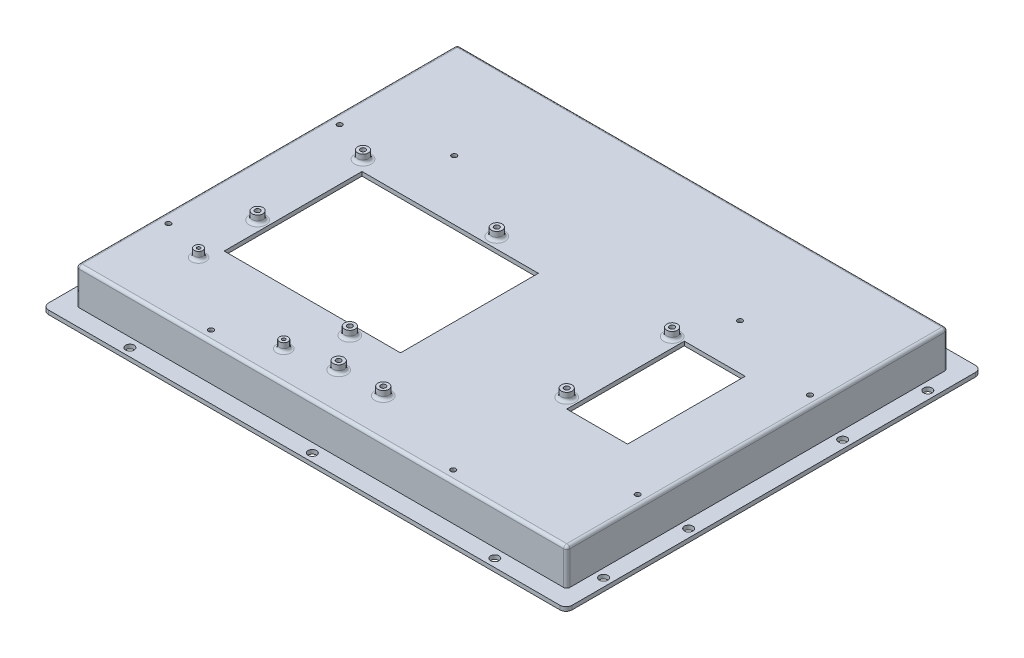
SolidWorks part; units mm, degrees
ref_plane "Front Plane" through (0, 0, 0) normal (0, 0, 1) x (1, 0, 0)
ref_plane "Top Plane" through (0, 0, 0) normal (0, 1, 0) x (1, 0, 0)
ref_plane "Right Plane" through (0, 0, 0) normal (1, 0, 0) x (0, 0, -1)
sketch "Sketch1" plane through (0, 0, 0) normal (0, 1, 0) x (1, 0, 0)
  line L1 (0, 0) -> (258.3, 0)
  line L2 (0, 0) -> (0, 205)
  line L3 (0, 205) -> (258.3, 205)
  line L4 (258.3, 0) -> (258.3, 205)
  dimension "D1" = 258.3
  dimension "D2" = 205
extrude "Boss-Extrude1" add sketch "Sketch1" along normal blind 20
sketch "Sketch2" plane through (0, 20, 0) normal (0, 1, 0) x (-1, 0, 0)
  line L0 (-129.15, 0) -> (-129.15, 18.2552) construction
  line L1 (-8.15, -8.5) -> (-250.15, -8.5)
  line L2 (-8.15, -8.5) -> (-8.15, -196.5)
  line L3 (-8.15, -196.5) -> (-250.15, -196.5)
  line L4 (-250.15, -8.5) -> (-250.15, -196.5)
  line L5 (0, 0) -> (-258.3, 0) construction
  line L6 (-258.3, -102.5) -> (-281.1398, -102.5) construction
  line L7 (-258.3, 0) -> (-258.3, -205) construction
  dimension "D1" = 242
  dimension "D2" = 188
extrude "Cut-Extrude1" cut sketch "Sketch2" against normal blind 18 flip side to cut
sketch "Sketch3" plane through (0, 0, 0) normal (0, -1, 0) x (1, 0, 0)
  line L0 (258.3, -102.5) -> (287.3168, -102.5) construction
  line L1 (248.15, -194.5) -> (10.15, -194.5)
  line L2 (248.15, -194.5) -> (248.15, -10.5)
  line L3 (248.15, -10.5) -> (10.15, -10.5)
  line L4 (10.15, -194.5) -> (10.15, -10.5)
  line L5 (258.3, 0) -> (258.3, -205) construction
  line L6 (129.15, -205) -> (129.15, -238.7281) construction
  line L8 (258.3, -205) -> (0, -205) construction
  dimension "D1" = 238
  dimension "D2" = 184
extrude "Cut-Extrude2" cut sketch "Sketch3" against normal blind 18
sketch "Sketch4" plane through (0, 20, 0) normal (0, 1, 0) x (1, 0, 0)
  line L0 (8.15, 196.5) -> (8.15, 8.5) construction
  line L1 (126.15, 50.5) -> (39.15, 50.5)
  line L2 (126.15, 50.5) -> (126.15, 118.5)
  line L3 (126.15, 118.5) -> (39.15, 118.5)
  line L4 (39.15, 50.5) -> (39.15, 118.5)
  line L5 (221.15, 67.5) -> (191.15, 67.5)
  line L6 (221.15, 67.5) -> (221.15, 125.5)
  line L7 (221.15, 125.5) -> (191.15, 125.5)
  line L8 (191.15, 67.5) -> (191.15, 125.5)
  line L9 (8.15, 8.5) -> (250.15, 8.5) construction
  line L10 (250.15, 8.5) -> (250.15, 196.5) construction
  dimension "D1" = 31
  dimension "D2" = 87
  dimension "D3" = 42
  dimension "D4" = 68
  dimension "D5" = 30
  dimension "D6" = 58
  dimension "D7" = 59
  dimension "D8" = 29
extrude "Cut-Extrude3" cut sketch "Sketch4" against normal through all
sketch "Sketch5" plane through (0, 20, 0) normal (0, 1, 0) x (1, 0, 0)
  line L0 (39.15, 50.5) -> (126.15, 50.5) construction
  line L1 (126.15, 50.5) -> (126.15, 118.5) construction
  line L2 (8.15, 8.5) -> (250.15, 8.5) construction
  line L3 (39.15, 118.5) -> (39.15, 50.5) construction
  line L4 (191.15, 125.5) -> (191.15, 67.5) construction
  line L5 (191.15, 67.5) -> (221.15, 67.5) construction
  line L6 (8.15, 196.5) -> (8.15, 8.5) construction
  circle A0 centre (34.15, 72) radius 2.65
  circle A1 centre (34.15, 124) radius 2.65
  circle A2 centre (100.15, 124) radius 2.65
  circle A3 centre (106.15, 45.5) radius 2.65
  circle A4 centre (186.15, 72.5) radius 2.65
  circle A5 centre (186.15, 124.5) radius 2.65
  circle A6 centre (118.15, 28) radius 2.65
  circle A7 centre (140.15, 28) radius 2.65
  dimension "D1" = 5.3
  dimension "D4" = 5
  dimension "D5" = 20
  dimension "D7" = 5
  dimension "D8" = 52
  dimension "D9" = 5
  dimension "D10" = 5
  dimension "D13" = 110
  dimension "D2" = 52
  dimension "D3" = 66
  dimension "D6" = 21.5
  dimension "D11" = 22
  dimension "D12" = 19.5
extrude "Boss-Extrude2" add sketch "Sketch5" along normal blind 4
sketch "Sketch6" plane through (0, 24, 0) normal (0, 1, 0) x (1, 0, 0)
  circle A0 centre (34.15, 124) radius 1.25
  circle A1 centre (100.15, 124) radius 1.25
  circle A2 centre (186.15, 124.5) radius 1.25
  circle A3 centre (186.15, 72.5) radius 1.25
  circle A4 centre (106.15, 45.5) radius 1.25
  circle A5 centre (34.15, 72) radius 1.25
  circle A6 centre (140.15, 28) radius 1.25
  circle A7 centre (118.15, 28) radius 1.25
  dimension "D1" = 2.5
extrude "Cut-Extrude4" cut sketch "Sketch6" against normal through all
sketch "Sketch7" plane through (0, 2, 0) normal (0, 1, 0) x (1, 0, 0)
  line L0 (0, 0) -> (258.3, 0) construction
  line L1 (258.3, 0) -> (258.3, 205) construction
  line L2 (0, 205) -> (0, 0) construction
  line L3 (258.3, 205) -> (0, 205) construction
  line L4 (258.3, 205) -> (0, 205) construction
  line L5 (129.15, 0) -> (129.15, -15.0933) construction
  line L7 (258.3, 102.5) -> (279.2876, 102.5) construction
  line L8 (0, 102.5) -> (-38.7144, 102.5) construction
  line L9 (129.15, 205) -> (129.15, 223.317) construction
  circle A0 centre (254.3, 22.5) radius 2.1
  circle A1 centre (254.3, 140.5) radius 2.1
  circle A2 centre (254.3, 182.5) radius 2.1
  circle A4 centre (219.15, 201) radius 2.1
  circle A5 centre (134.15, 201) radius 2.1
  circle A6 centre (124.15, 201) radius 2.1
  circle A7 centre (39.15, 201) radius 2.1
  circle A9 centre (4, 182.5) radius 2.1
  circle A10 centre (4, 102.5) radius 2.1
  circle A11 centre (4, 22.5) radius 2.1
  circle A12 centre (219.15, 4) radius 2.1
  circle A13 centre (129.15, 4) radius 2.1
  circle A14 centre (39.15, 4) radius 2.1
  circle A15 centre (254.3, 64.5) radius 2.1
  dimension "D1" = 4.2
  dimension "D2" = 4
  dimension "D3" = 4
  dimension "D6" = 90
  dimension "D7" = 90
  dimension "D13" = 10
  dimension "D14" = 4.2
  dimension "D16" = 85
  dimension "D4" = 4
  dimension "D5" = 4
  dimension "D8" = 42
  dimension "D9" = 42
  dimension "D10" = 76
  dimension "D11" = 80
  dimension "D12" = 80
extrude "Cut-Extrude5" cut sketch "Sketch7" against normal through all
sketch "Sketch8" plane through (0, 20, 0) normal (0, 1, 0) x (1, 0, 0)
  circle A0 centre (55.15, 148) radius 1.25
  circle A1 centre (13.65, 133) radius 1.25
  circle A2 centre (13.65, 48.5) radius 1.25
  circle A3 centre (69.65, 13.5) radius 1.25
  circle A4 centre (189.15, 13.5) radius 1.25
  circle A5 centre (245.15, 48.5) radius 1.25
  circle A6 centre (245.15, 133.5) radius 1.25
  circle A7 centre (196.15, 148) radius 1.25
  dimension "D1" = 2.5
extrude "Cut-Extrude6" cut sketch "Sketch8" against normal through all
sketch "Sketch9" plane through (0, 18, 0) normal (0, -1, 0) x (1, 0, 0)
  circle A0 centre (13.65, -48.5) radius 3
  circle A1 centre (69.65, -13.5) radius 3
  circle A2 centre (189.15, -13.5) radius 3
  circle A3 centre (245.15, -48.5) radius 3
  circle A4 centre (245.15, -133.5) radius 3
  circle A5 centre (196.15, -148) radius 3
  circle A6 centre (55.15, -148) radius 3
  circle A7 centre (13.65, -133) radius 3
  circle A8 centre (13.65, -133) radius 1.25
  circle A9 centre (55.15, -148) radius 1.25
  circle A10 centre (196.15, -148) radius 1.25
  circle A11 centre (245.15, -133.5) radius 1.25
  circle A12 centre (245.15, -48.5) radius 1.25
  circle A13 centre (189.15, -13.5) radius 1.25
  circle A14 centre (69.65, -13.5) radius 1.25
  circle A15 centre (13.65, -48.5) radius 1.25
  dimension "D1" = 6
extrude "Boss-Extrude5" add sketch "Sketch9" along normal blind 2 and the other way blind 1 separate body
sketch "Sketch10" plane through (0, 0, 0) normal (0, -1, 0) x (1, 0, 0)
  line L0 (129.15, -10.5) -> (129.15, 23.0959) construction
  line L1 (8.15, -8.25) -> (20.15, -8.25)
  line L2 (8.15, -8.25) -> (8.15, -23.25)
  line L3 (8.15, -23.25) -> (20.15, -23.25)
  line L4 (20.15, -8.25) -> (20.15, -23.25)
  line L5 (119.15, -8.25) -> (139.15, -8.25)
  line L6 (119.15, -8.25) -> (119.15, -20.25)
  line L7 (119.15, -20.25) -> (139.15, -20.25)
  line L8 (139.15, -8.25) -> (139.15, -20.25)
  line L9 (238.15, -8.25) -> (250.15, -8.25)
  line L10 (238.15, -8.25) -> (238.15, -23.25)
  line L11 (238.15, -23.25) -> (250.15, -23.25)
  line L12 (250.15, -8.25) -> (250.15, -23.25)
  line L13 (8.15, -181.75) -> (20.15, -181.75)
  line L14 (8.15, -181.75) -> (8.15, -196.75)
  line L15 (8.15, -196.75) -> (20.15, -196.75)
  line L16 (20.15, -181.75) -> (20.15, -196.75)
  line L17 (146.15, -184.75) -> (181.15, -184.75)
  line L18 (146.15, -184.75) -> (146.15, -196.75)
  line L19 (146.15, -196.75) -> (181.15, -196.75)
  line L20 (181.15, -184.75) -> (181.15, -196.75)
  line L21 (238.15, -181.75) -> (250.15, -181.75)
  line L22 (238.15, -181.75) -> (238.15, -196.75)
  line L23 (238.15, -196.75) -> (250.15, -196.75)
  line L24 (250.15, -181.75) -> (250.15, -196.75)
  line L25 (248.15, -10.5) -> (10.15, -10.5) construction
  line L26 (10.15, -102.5) -> (-14.0756, -102.5) construction
  line L27 (10.15, -10.5) -> (10.15, -194.5) construction
  line L28 (248.15, -194.5) -> (248.15, -10.5) construction
  line L29 (10.15, -60) -> (20.15, -60)
  line L30 (10.15, -60) -> (10.15, -75)
  line L31 (10.15, -75) -> (20.15, -75)
  line L32 (20.15, -60) -> (20.15, -75)
  line L33 (10.15, -130) -> (20.15, -130)
  line L34 (10.15, -130) -> (10.15, -145)
  line L35 (10.15, -145) -> (20.15, -145)
  line L36 (20.15, -130) -> (20.15, -145)
  line L37 (248.15, -60) -> (238.15, -60)
  line L38 (248.15, -60) -> (248.15, -75)
  line L39 (248.15, -75) -> (238.15, -75)
  line L40 (238.15, -60) -> (238.15, -75)
  line L41 (248.15, -10.5) -> (10.15, -10.5) construction
  line L42 (248.15, -130) -> (238.15, -130)
  line L43 (248.15, -130) -> (248.15, -145)
  line L44 (248.15, -145) -> (238.15, -145)
  line L45 (238.15, -130) -> (238.15, -145)
  line L46 (56.65, -10.5) -> (76.65, -10.5)
  line L47 (56.65, -10.5) -> (56.65, -20.25)
  line L48 (56.65, -20.25) -> (76.65, -20.25)
  line L49 (76.65, -10.5) -> (76.65, -20.25)
  line L50 (10.15, -194.5) -> (248.15, -194.5) construction
  line L51 (181.65, -10.5) -> (201.65, -10.5)
  line L52 (181.65, -10.5) -> (181.65, -20.25)
  line L53 (181.65, -20.25) -> (201.65, -20.25)
  line L54 (201.65, -10.5) -> (201.65, -20.25)
  line L55 (77.15, -194.5) -> (112.15, -194.5)
  line L56 (77.15, -194.5) -> (77.15, -184.75)
  line L57 (77.15, -184.75) -> (112.15, -184.75)
  line L58 (112.15, -194.5) -> (112.15, -184.75)
  line L59 (10.15, -194.5) -> (248.15, -194.5) construction
  line L60 (218.15, -194.5) -> (230.15, -194.5)
  line L61 (218.15, -194.5) -> (218.15, -184.75)
  line L62 (218.15, -184.75) -> (230.15, -184.75)
  line L63 (230.15, -194.5) -> (230.15, -184.75)
  line L65 (28.15, -194.5) -> (40.15, -194.5)
  line L66 (28.15, -194.5) -> (28.15, -184.75)
  line L67 (28.15, -184.75) -> (40.15, -184.75)
  line L68 (40.15, -194.5) -> (40.15, -184.75)
  dimension "D1" = 242
  dimension "D2" = 20
  dimension "D3" = 12
  dimension "D4" = 12
  dimension "D5" = 188.5
  dimension "D6" = 15
  dimension "D7" = 15
  dimension "D8" = 55
  dimension "D9" = 12
  dimension "D10" = 12
  dimension "D11" = 105
  dimension "D12" = 12
  dimension "D13" = 20
  dimension "D14" = 37
  dimension "D15" = 35
  dimension "D16" = 35
  dimension "D17" = 20
  dimension "D18" = 12
  dimension "D19" = 37
extrude "Boss-Extrude6" add sketch "Sketch10" against normal blind 5
sketch "Sketch11" plane through (0, 0, 0) normal (0, -1, 0) x (1, 0, 0)
  line L0 (129.15, -205) -> (129.15, -225.0938) construction
  line L1 (8.25, -196.9) -> (250.05, -196.9)
  line L2 (8.25, -196.9) -> (8.25, -8.1)
  line L3 (8.25, -8.1) -> (250.05, -8.1)
  line L4 (250.05, -196.9) -> (250.05, -8.1)
  line L5 (258.3, -205) -> (0, -205) construction
  line L6 (0, -102.5) -> (-17.0055, -102.5) construction
  line L7 (0, -205) -> (0, 0) construction
  dimension "D1" = 241.8
  dimension "D2" = 188.8
extrude "Boss-Extrude7" add sketch "Sketch11" along normal blind 2
sketch "Sketch12" plane through (0, -2, 0) normal (0, -1, 0) x (1, 0, 0)
  line L0 (8.25, -102.5) -> (16.7491, -102.5) construction
  line L1 (16.65, -15.75) -> (241.65, -15.75)
  line L2 (16.65, -15.75) -> (16.65, -189.25)
  line L3 (16.65, -189.25) -> (241.65, -189.25)
  line L4 (241.65, -15.75) -> (241.65, -189.25)
  line L5 (8.25, -8.1) -> (8.25, -196.9) construction
  line L6 (129.15, -8.1) -> (129.15, 15.7162) construction
  line L7 (250.05, -8.1) -> (8.25, -8.1) construction
  dimension "D1" = 225
  dimension "D2" = 173.5
extrude "Cut-Extrude7" cut sketch "Sketch12" against normal up to surface (2 mm away) up to face at (129.15, 0, -108.7232)
sketch "Sketch13" plane through (0, 0, -196.75) normal (0, 0, -1) x (-1, 0, 0)
  line L0 (-146.15, 5) -> (-181.15, 5) construction
  line L1 (-119.1526, 5) -> (-181.15, 5)
  line L2 (-119.1526, 5) -> (-119.1526, 2)
  line L3 (-119.1526, 2) -> (-181.15, 2)
  line L4 (-181.15, 5) -> (-181.15, 2)
  line L5 (-181.15, 2) -> (-181.15, 5) construction
  line L7 (-8.15, 5) -> (-20.15, 5)
  line L8 (-8.15, 5) -> (-8.15, 2)
  line L9 (-8.15, 2) -> (-20.15, 2)
  line L10 (-20.15, 5) -> (-20.15, 2)
  line L11 (-238.15, 5) -> (-250.15, 5)
  line L12 (-238.15, 5) -> (-238.15, 2)
  line L13 (-238.15, 2) -> (-250.15, 2)
  line L14 (-250.15, 5) -> (-250.15, 2)
extrude "Cut-Extrude8" cut sketch "Sketch13" against normal up to surface (0.25 mm away) up to face at (140.65, 6.5, -196.5)
sketch "Sketch14" plane through (0, 0, -8.25) normal (0, 0, 1) x (1, 0, 0)
  line L1 (139.15, 5) -> (119.15, 5)
  line L2 (139.15, 5) -> (139.15, 2)
  line L3 (139.15, 2) -> (119.15, 2)
  line L4 (119.15, 5) -> (119.15, 2)
  line L5 (250.15, 5) -> (238.15, 5)
  line L6 (250.15, 5) -> (250.15, 2)
  line L7 (250.15, 2) -> (238.15, 2)
  line L8 (238.15, 5) -> (238.15, 2)
  line L9 (20.15, 5) -> (8.15, 5)
  line L10 (20.15, 5) -> (20.15, 2)
  line L11 (20.15, 2) -> (8.15, 2)
  line L12 (8.15, 5) -> (8.15, 2)
extrude "Cut-Extrude9" cut sketch "Sketch14" against normal up to surface (0.25 mm away) up to face at (129.15, 6.5, -8.5)
sketch "Sketch15" plane through (0, -2, 0) normal (0, -1, 0) x (1, 0, 0)
  line L0 (16.65, -15.75) -> (16.65, -189.25) construction
  line L1 (16.65, -33.75) -> (11.15, -33.75)
  line L2 (16.65, -33.75) -> (16.65, -44.05)
  line L3 (16.65, -44.05) -> (11.15, -44.05)
  line L4 (11.15, -33.75) -> (11.15, -44.05)
  line L5 (241.65, -189.25) -> (241.65, -15.75) construction
  line L6 (16.65, -171.25) -> (11.15, -171.25)
  line L7 (16.65, -171.25) -> (16.65, -160.95)
  line L8 (16.65, -160.95) -> (11.15, -160.95)
  line L9 (11.15, -171.25) -> (11.15, -160.95)
  line L10 (241.65, -171.25) -> (247.15, -171.25)
  line L11 (241.65, -171.25) -> (241.65, -160.95)
  line L12 (241.65, -160.95) -> (247.15, -160.95)
  line L13 (247.15, -171.25) -> (247.15, -160.95)
  line L14 (241.65, -15.75) -> (16.65, -15.75) construction
  line L15 (241.65, -33.75) -> (247.15, -33.75)
  line L16 (241.65, -33.75) -> (241.65, -44.05)
  line L17 (241.65, -44.05) -> (247.15, -44.05)
  line L18 (247.15, -33.75) -> (247.15, -44.05)
  line L20 (250.05, -102.5) -> (270.737, -102.5) construction
  line L21 (250.05, -196.9) -> (250.05, -8.1) construction
  dimension "D1" = 10.3
  dimension "D2" = 18
  dimension "D3" = 10.3
  dimension "D5" = 5.5
extrude "Cut-Extrude10" cut sketch "Sketch15" against normal blind 1.4
sketch "Sketch16" plane through (0, -2, 0) normal (0, -1, 0) x (1, 0, 0)
  line L0 (16.65, -44.05) -> (16.65, -160.95) construction
  line L1 (16.65, -127.5) -> (8.25, -127.5)
  line L2 (16.65, -127.5) -> (16.65, -77.5)
  line L3 (16.65, -77.5) -> (8.25, -77.5)
  line L4 (8.25, -127.5) -> (8.25, -77.5)
  line L5 (8.25, -8.1) -> (8.25, -196.9) construction
  line L6 (8.25, -102.5) -> (-10.5058, -102.5) construction
  dimension "D1" = 50
extrude "Cut-Extrude11" cut sketch "Sketch16" against normal up to surface (2 mm away) up to face at (129.15, 0, -191.875)
sketch "Sketch17" plane through (0, 20, 0) normal (0, 1, 0) x (1, 0, 0)
  line L0 (8.15, 8.5) -> (250.15, 8.5) construction
  circle A0 centre (35.55, 41.5) radius 2.1
  circle A1 centre (106.15, 45.5) radius 2.65 construction
  circle A2 centre (95.55, 23.5) radius 2.1
  dimension "D1" = 4.2
  dimension "D2" = 70.6
  dimension "D3" = 33
  dimension "D4" = 15
  dimension "D5" = 60
extrude "Boss-Extrude8" add sketch "Sketch17" along normal up to surface (4 mm away) up to face at (34.15, 24, -70.75)
sketch "Sketch18" plane through (0, 24, 0) normal (0, 1, 0) x (1, 0, 0)
  circle A0 centre (35.55, 41.5) radius 0.8
  circle A1 centre (95.55, 23.5) radius 0.8
  dimension "D1" = 1.6
extrude "Cut-Extrude12" cut sketch "Sketch18" against normal through all
sketch "Sketch19" plane through (0, 0, 0) normal (0, -1, 0) x (1, 0, 0)
  line L1 (16.65, -15.75) -> (241.65, -15.75)
  line L2 (16.65, -15.75) -> (16.65, -189.25)
  line L3 (16.65, -189.25) -> (241.65, -189.25)
  line L4 (241.65, -15.75) -> (241.65, -189.25)
extrude "Cut-Extrude13" cut sketch "Sketch19" against normal blind 1.7
fillet "Fillet1" radius 1 12 edges at (248.15, 18, -102.5) (129.15, 18, -10.5) (10.15, 11.5, -10.5) (129.15, 18, -194.5) (10.15, 11.5, -194.5) (248.15, 11.5, -194.5) (10.15, 18, -102.5) (248.15, 11.5, -10.5) (250.05, -1, -196.9) (250.05, -1, -8.1) (8.25, -1, -8.1) (8.25, -1, -196.9)
fillet "Fillet2" radius 1.5 18 edges at (250.15, 20, -102.5) (250.15, 11, -196.5) (129.15, 20, -196.5) (129.15, 20, -8.5) (8.15, 20, -102.5) (8.15, 11, -196.5) (8.15, 11, -8.5) (250.15, 11, -8.5) (34.15, 20, -126.65) (34.15, 20, -74.65) (35.55, 20, -43.6) (106.15, 20, -48.15) (100.15, 20, -126.65) (186.15, 20, -75.15) (186.15, 20, -127.15) (140.15, 20, -30.65) (118.15, 20, -30.65) (95.55, 20, -25.6)
fillet "Fillet3" radius 3 4 edges at (258.3, 1, 0) (258.3, 1, -205) (0, 1, -205) (0, 1, 0)
